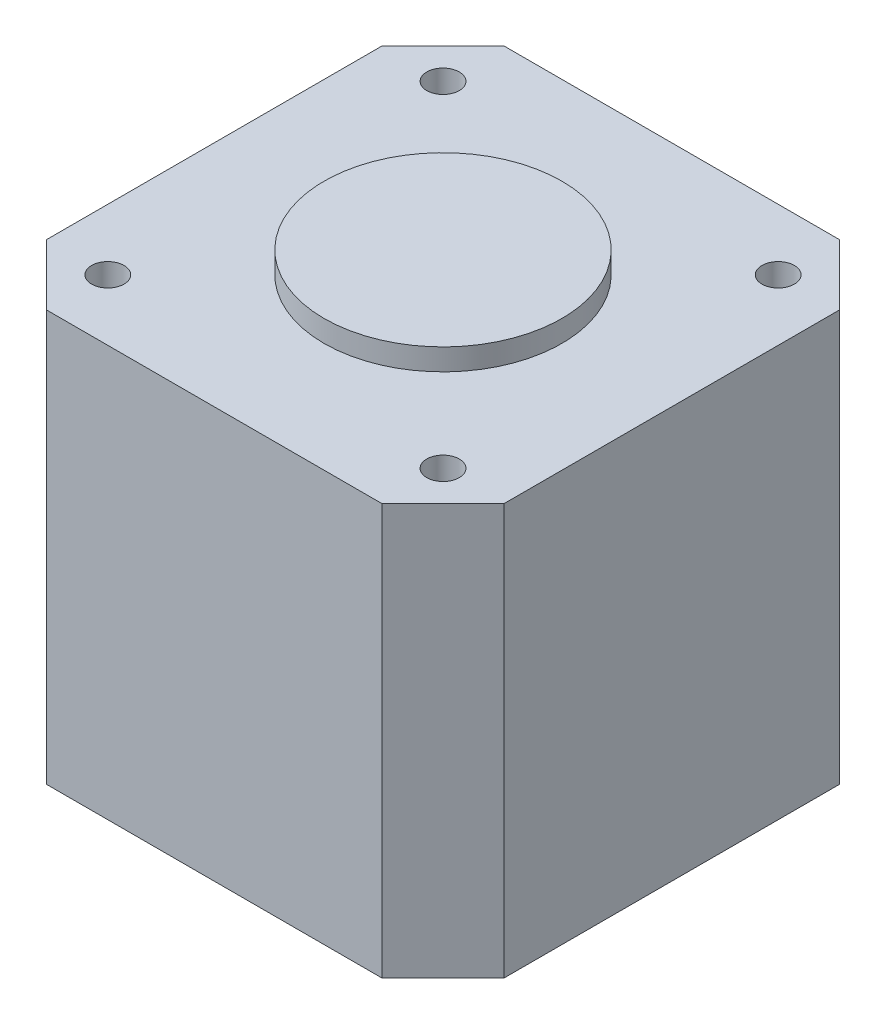
SolidWorks part; units mm, degrees
ref_plane "前视基准面" through (0, 0, 0) normal (0, 0, 1) x (1, 0, 0)
ref_plane "上视基准面" through (0, 0, 0) normal (0, 1, 0) x (1, 0, 0)
ref_plane "右视基准面" through (0, 0, 0) normal (1, 0, 0) x (0, 0, -1)
sketch "草图2" plane through (0, 0, 0) normal (0, 1, 0) x (1, 0, 0)
  line L0 (-15.5, 21.15) -> (-21.15, 15.5)
  line L1 (-15.5, 21.15) -> (15.5, 21.15)
  line L2 (-21.15, 15.5) -> (-21.15, -15.5)
  line L3 (-15.5, -21.15) -> (15.5, -21.15)
  line L4 (21.15, 15.5) -> (21.15, -15.5)
  line L5 (-21.15, 21.15) -> (21.15, -21.15) construction
  line L6 (-21.15, -21.15) -> (21.15, 21.15) construction
  line L7 (-21.15, -15.5) -> (-15.5, -21.15)
  line L8 (15.5, -21.15) -> (21.15, -15.5)
  line L9 (15.5, 21.15) -> (21.15, 15.5)
  point P0 (0, 0)
  dimension "D1" = 42.3
  dimension "D2" = 42.3
  dimension "D3" = 5.65
  dimension "D4" = 5.65
  dimension "D5" = 5.65
  dimension "D6" = 5.65
extrude "凸台-拉伸1" add sketch "草图2" along normal blind 38
sketch "草图3" plane through (0, 38, 0) normal (0, 1, 0) x (1, 0, 0)
  circle A0 centre (0, 0) radius 11
  dimension "D1" = 22
extrude "凸台-拉伸2" add sketch "草图3" along normal blind 2
sketch "草图14" plane through (0, 40, 0) normal (0, 1, 0) x (1, 0, 0)
  circle A0 centre (0, 0) radius 2.5
  dimension "D1" = 5
sketch "草图15" plane through (0, 38, 0) normal (0, 1, 0) x (1, 0, 0)
  line L0 (-15.5, 15.5) -> (-15.5, -15.5) construction
  circle A0 centre (-15.5, 15.5) radius 1.5
  circle A1 centre (15.5, 15.5) radius 1.5
  circle A2 centre (15.5, -15.5) radius 1.5
  circle A3 centre (-15.5, -15.5) radius 1.5
  point P11 (0, 0)
  dimension "D3" = 3
  dimension "D2" = 31
  dimension "D4" = 31
  dimension "D1" = 4
extrude "切除-拉伸1" cut sketch "草图15" against normal blind 5
